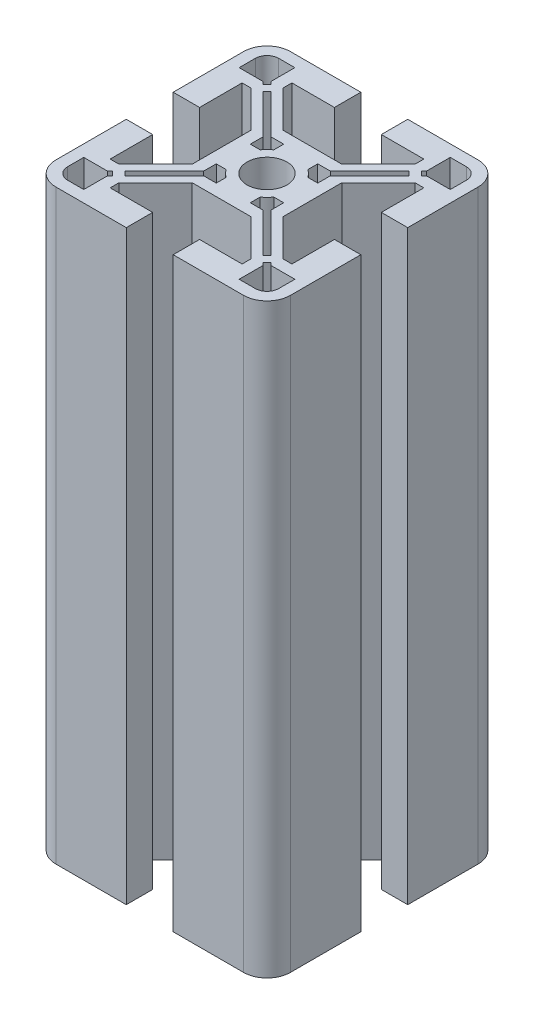
SolidWorks part; units mm, degrees
ref_plane "Ebene vorne" through (0, 0, 0) normal (0, 0, 1) x (1, 0, 0)
ref_plane "Ebene oben" through (0, 0, 0) normal (0, 1, 0) x (1, 0, 0)
ref_plane "Ebene rechts" through (0, 0, 0) normal (1, 0, 0) x (0, 0, -1)
sketch "Sketch1" plane through (0, 0, 0) normal (0, 1, 0) x (1, 0, 0)
  line L0 (0, 0) -> (-50.9364, 0) construction
  line L1 (0, 0) -> (0, 54.6457) construction
  line L2 (0, 0) -> (-54.6457, 54.6457) construction
  line L3 (-20, 4) -> (-20, 16)
  line L4 (-20, 4) -> (-15.5, 4)
  line L5 (-15.5, 4) -> (-15.5, 11.25)
  line L6 (-15.5, 11.25) -> (-14, 11.25)
  line L7 (-14, 11.25) -> (-7.75, 5)
  line L8 (-7.75, 5) -> (-7.75, 0)
  line L9 (-18, 13.25) -> (-18, 16)
  line L10 (-18, 13.25) -> (-13.9571, 13.25)
  line L11 (-13.5089, 12.8018) -> (-12.8018, 13.5089)
  line L12 (-13.5089, 12.8018) -> (-13.9571, 13.25)
  line L13 (-12.4482, 11.7411) -> (-5.75, 5.0429)
  line L14 (-5.75, 5.0429) -> (-5.75, 2.9047)
  line L15 (-12.4482, 11.7411) -> (-11.7411, 12.4482)
  line L16 (-5.75, 2.9047) -> (-5.25, 2.9047)
  line L17 (-11.7411, 12.4482) -> (-5.0429, 5.75)
  line L18 (-2.9047, 5.75) -> (-2.9047, 5.25)
  line L19 (-5.0429, 5.75) -> (-2.9047, 5.75)
  line L20 (-13.25, 18) -> (-13.25, 13.9571)
  line L21 (-13.25, 18) -> (-16, 18)
  line L22 (-11.25, 14) -> (-5, 7.75)
  line L23 (-4, 20) -> (-4, 15.5)
  line L24 (-11.25, 15.5) -> (-11.25, 14)
  line L25 (-5, 7.75) -> (0, 7.75)
  line L26 (-4, 15.5) -> (-11.25, 15.5)
  line L27 (-4, 20) -> (-16, 20)
  line L28 (15.5, 4) -> (15.5, 11.25)
  line L29 (20, 4) -> (20, 16)
  line L30 (20, 4) -> (15.5, 4)
  line L31 (18, 13.25) -> (18, 16)
  line L32 (18, 13.25) -> (13.9571, 13.25)
  line L33 (14, 11.25) -> (7.75, 5)
  line L34 (15.5, 11.25) -> (14, 11.25)
  line L35 (7.75, 5) -> (7.75, 0)
  line L36 (5.75, 5.0429) -> (5.75, 2.9047)
  line L37 (11.7411, 12.4482) -> (5.0429, 5.75)
  line L38 (12.4482, 11.7411) -> (5.75, 5.0429)
  line L39 (5.0429, 5.75) -> (2.9047, 5.75)
  line L40 (2.9047, 5.75) -> (2.9047, 5.25)
  line L41 (5.75, 2.9047) -> (5.25, 2.9047)
  line L42 (5, 7.75) -> (0, 7.75)
  line L43 (11.25, 14) -> (5, 7.75)
  line L44 (13.25, 18) -> (13.25, 13.9571)
  line L45 (13.25, 18) -> (16, 18)
  line L46 (4, 15.5) -> (11.25, 15.5)
  line L47 (11.25, 15.5) -> (11.25, 14)
  line L48 (4, 20) -> (16, 20)
  line L49 (4, 20) -> (4, 15.5)
  line L50 (4, -15.5) -> (11.25, -15.5)
  line L51 (4, -20) -> (16, -20)
  line L52 (4, -20) -> (4, -15.5)
  line L53 (13.25, -18) -> (16, -18)
  line L54 (13.25, -18) -> (13.25, -13.9571)
  line L55 (11.25, -14) -> (5, -7.75)
  line L56 (11.25, -15.5) -> (11.25, -14)
  line L57 (5, -7.75) -> (0, -7.75)
  line L58 (5.0429, -5.75) -> (2.9047, -5.75)
  line L59 (12.4482, -11.7411) -> (5.75, -5.0429)
  line L60 (11.7411, -12.4482) -> (5.0429, -5.75)
  line L61 (5.75, -5.0429) -> (5.75, -2.9047)
  line L62 (5.75, -2.9047) -> (5.25, -2.9047)
  line L63 (2.9047, -5.75) -> (2.9047, -5.25)
  line L64 (7.75, -5) -> (7.75, 0)
  line L65 (14, -11.25) -> (7.75, -5)
  line L66 (18, -13.25) -> (13.9571, -13.25)
  line L67 (18, -13.25) -> (18, -16)
  line L68 (15.5, -4) -> (15.5, -11.25)
  line L69 (15.5, -11.25) -> (14, -11.25)
  line L70 (20, -4) -> (20, -16)
  line L71 (20, -4) -> (15.5, -4)
  line L72 (-15.5, -4) -> (-15.5, -11.25)
  line L73 (-20, -4) -> (-20, -16)
  line L74 (-20, -4) -> (-15.5, -4)
  line L75 (-18, -13.25) -> (-18, -16)
  line L76 (-18, -13.25) -> (-13.9571, -13.25)
  line L77 (-14, -11.25) -> (-7.75, -5)
  line L78 (-15.5, -11.25) -> (-14, -11.25)
  line L79 (-7.75, -5) -> (-7.75, 0)
  line L80 (-5.75, -5.0429) -> (-5.75, -2.9047)
  line L81 (-11.7411, -12.4482) -> (-5.0429, -5.75)
  line L82 (-12.4482, -11.7411) -> (-5.75, -5.0429)
  line L83 (-5.0429, -5.75) -> (-2.9047, -5.75)
  line L84 (-2.9047, -5.75) -> (-2.9047, -5.25)
  line L85 (-5.75, -2.9047) -> (-5.25, -2.9047)
  line L86 (-5, -7.75) -> (0, -7.75)
  line L87 (-11.25, -14) -> (-5, -7.75)
  line L88 (-13.25, -18) -> (-13.25, -13.9571)
  line L89 (-13.25, -18) -> (-16, -18)
  line L90 (-4, -15.5) -> (-11.25, -15.5)
  line L91 (-11.25, -15.5) -> (-11.25, -14)
  line L92 (-4, -20) -> (-16, -20)
  line L93 (-4, -20) -> (-4, -15.5)
  line L94 (-12.8018, 13.5089) -> (-13.25, 13.9571)
  line L95 (12.8018, 13.5089) -> (13.25, 13.9571)
  line L96 (12.8018, 13.5089) -> (13.5089, 12.8018)
  line L97 (13.5089, 12.8018) -> (13.9571, 13.25)
  line L98 (11.7411, 12.4482) -> (12.4482, 11.7411)
  line L99 (13.5089, -12.8018) -> (13.9571, -13.25)
  line L100 (13.5089, -12.8018) -> (12.8018, -13.5089)
  line L101 (12.8018, -13.5089) -> (13.25, -13.9571)
  line L102 (12.4482, -11.7411) -> (11.7411, -12.4482)
  line L103 (-12.8018, -13.5089) -> (-13.25, -13.9571)
  line L104 (-12.8018, -13.5089) -> (-13.5089, -12.8018)
  line L105 (-13.5089, -12.8018) -> (-13.9571, -13.25)
  line L106 (-11.7411, -12.4482) -> (-12.4482, -11.7411)
  line L107 (-5.25, 2.9047) -> (-4.0697, 2.9047)
  line L108 (-2.9047, 5.25) -> (-2.9047, 4.0697)
  line L109 (2.9047, 5.25) -> (2.9047, 4.0697)
  line L110 (5.25, 2.9047) -> (4.0697, 2.9047)
  line L111 (5.25, -2.9047) -> (4.0697, -2.9047)
  line L112 (2.9047, -5.25) -> (2.9047, -4.0697)
  line L113 (-2.9047, -5.25) -> (-2.9047, -4.0697)
  line L114 (-5.25, -2.9047) -> (-4.0697, -2.9047)
  arc A0 (-20, 16) -> (-16, 20) centre (-16, 16) cw
  arc A1 (-18, 16) -> (-16, 18) centre (-16, 16) cw
  arc A2 (-3.4, 0) -> (0, 3.4) centre (0, 0) cw
  arc A3 (-4.0697, -2.9047) -> (-2.9047, -4.0697) centre (0, 0) ccw
  arc A4 (16, 20) -> (20, 16) centre (16, 16) cw
  arc A5 (16, 18) -> (18, 16) centre (16, 16) cw
  arc A6 (2.9047, -4.0697) -> (4.0697, -2.9047) centre (0, 0) ccw
  arc A7 (0, 3.4) -> (3.4, 0) centre (0, 0) cw
  arc A8 (20, -16) -> (16, -20) centre (16, -16) cw
  arc A9 (18, -16) -> (16, -18) centre (16, -16) cw
  arc A10 (4.0697, 2.9047) -> (2.9047, 4.0697) centre (0, 0) ccw
  arc A11 (3.4, 0) -> (0, -3.4) centre (0, 0) cw
  arc A12 (-16, -20) -> (-20, -16) centre (-16, -16) cw
  arc A13 (-16, -18) -> (-18, -16) centre (-16, -16) cw
  arc A14 (-2.9047, 4.0697) -> (-4.0697, 2.9047) centre (0, 0) ccw
  arc A15 (0, -3.4) -> (-3.4, 0) centre (0, 0) cw
  point P21 (-12.0947, 12.0947)
  point P43 (-13.1553, 13.1553)
  point P147 (0, 0)
  point P160 (0, 0)
  point P167 (0, 0)
  dimension "D3" = 4
  dimension "D9" = 0.5
  dimension "2" = 2
  dimension "D12" = 3.4
  dimension "D13" = 10
  dimension "D1" = 45
  dimension "D2" = 20
  dimension "D4" = 4
  dimension "D5" = 4.5
  dimension "D6" = 5
  dimension "D7" = 12.25
  dimension "D8" = 1.5
  dimension "D10" = 0.75
  dimension "D11" = 2
  dimension "D14" = 0.5
  dimension "D15" = 2
  dimension "D16" = 1.5
  dimension "D17" = 0.5
  dimension "D18" = 4
  dimension "D19" = 4
  dimension "D20" = 4
extrude "Boss-Extrude1" add sketch "Sketch1" along normal blind 100
